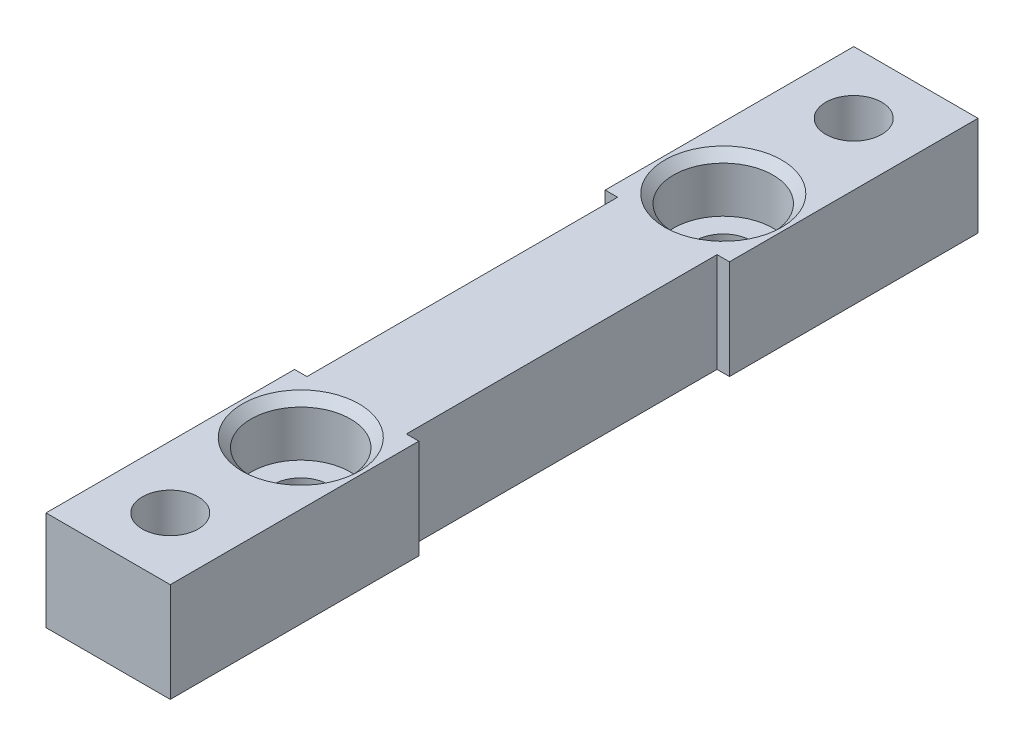
SolidWorks part; units mm, degrees
ref_plane "정면" through (0, 0, 0) normal (0, 0, 1) x (1, 0, 0)
ref_plane "윗면" through (0, 0, 0) normal (0, 1, 0) x (1, 0, 0)
ref_plane "우측면" through (0, 0, 0) normal (1, 0, 0) x (0, 0, -1)
sketch "스케치1" plane through (0, 0, 0) normal (0, 1, 0) x (1, 0, 0)
  line L0 (0, -17) -> (0, 17)
  line L14 (-5, 32.5) -> (5, 32.5)
  line L15 (-5, 32.5) -> (-5, 12.5)
  line L16 (-5, 12.5) -> (5, 12.5)
  line L17 (5, 32.5) -> (5, 12.5)
  line L18 (-5, 32.5) -> (5, 12.5) construction
  line L19 (-5, 12.5) -> (5, 32.5) construction
  line L20 (-4, 12.5) -> (4, 12.5)
  line L21 (-4, 12.5) -> (-4, -12.5)
  line L22 (-4, 0) -> (4, 0)
  line L23 (4, 12.5) -> (4, -12.5)
  line L24 (-4, 12.5) -> (4, 0) construction
  line L25 (-4, 0) -> (4, 12.5) construction
  line L26 (-4, 0) -> (4, -12.5) construction
  line L27 (-4, -12.5) -> (4, 0) construction
  line L28 (-5, -12.5) -> (5, -32.5) construction
  line L29 (-5, -32.5) -> (5, -12.5) construction
  line L30 (-4, -12.5) -> (4, -12.5)
  line L31 (5, -32.5) -> (5, -12.5)
  line L32 (-5, -12.5) -> (5, -12.5)
  line L33 (-5, -32.5) -> (-5, -12.5)
  line L34 (-5, -32.5) -> (5, -32.5)
  point P0 (0, 22.5)
  point P5 (0, 6.25)
  point P18 (0, -6.25)
  point P20 (0, 0)
  point P21 (0, -22.5)
  dimension "D1" = 10
  dimension "D2" = 20
  dimension "D3" = 32.5
  dimension "D4" = 8
  dimension "D5" = 17
extrude "보스-돌출1" add sketch "스케치1" along normal blind 8
hole_wizard "M4 육각 소켓 머리 캡 나사용 카운터보어1" positions "스케치2" profile "스케치3" counterbore size "M4" standard "ISO" end condition up to next
sketch "스케치2" plane through (0, 8, 0) normal (0, 1, 0) x (1, 0, 0)
  line L0 (0, 17) -> (0, -17)
  line L2 (4, 12.5) -> (4, -12.5) construction
  line L3 (4, 12.5) -> (4, -12.5)
  point P1 (0, 17)
  point P2 (0, -17)
  point P13 (4, 0)
  point P14 (0, 0)
  dimension "D1" = 34
sketch "스케치3" plane through (0, 8, -17) normal (1, 0, 0) x (0, 0, 1)
  line L0 (0, 0) -> (0, 8)
  line L1 (0, 8) -> (2.25, 8)
  line L3 (2.25, 8) -> (2.25, 4.4)
  line L4 (4, 4.4) -> (2.25, 4.4)
  line L5 (4, 4.4) -> (4, 0.7)
  line L6 (4, 0.7) -> (4.7, 0)
  line L7 (4.7, 0) -> (0, 0)
  line L8 (-4, 0.7) -> (-4.7, 0) construction
  line L11 (0, -6.35) -> (0, 107.95) construction
  dimension "관통 구멍 지름" = 4.5
  dimension "관통 구멍 깊이" = 8
  dimension "카운터보어 지름" = 8
  dimension "카운터보어 깊이" = 4.4
  dimension "표면 카운터싱크 지름" = 9.4
  dimension "표면 카운터싱크 각도" = 90
hole_wizard "M4 여유 구멍1" positions "스케치4" profile "스케치6" hole size "M4" standard "ISO" end condition up to next
sketch "스케치4" plane through (0, 0, 0) normal (0, -1, 0) x (-1, 0, 0)
  line L0 (0, -27.5) -> (0, 27.5)
  line L2 (-4, 12.5) -> (-4, -12.5) construction
  line L3 (-4, 12.5) -> (-4, -12.5)
  point P1 (0, -27.5)
  point P2 (0, 27.5)
  point P7 (0, 0)
  point P8 (-4, 0)
  point P13 (54.1084, -109.4208)
  dimension "D1" = 55
sketch "스케치6" plane through (0, 0, 27.5) normal (1, 0, 0) x (0, 0, -1)
  line L0 (0, 0) -> (0, 8)
  line L1 (0, 8) -> (2.25, 8)
  line L2 (2.25, 8) -> (2.25, 0)
  line L5 (2.25, 0) -> (0, 0)
  line L11 (0, -6.35) -> (0, 107.95) construction
  dimension "관통 구멍 지름" = 4.5
  dimension "관통 구멍 깊이" = 8
sketch "스케치7" plane through (0, 0, 0) normal (0, -1, 0) x (1, 0, 0)
  line L0 (-5, -32.5) -> (5, -32.5) construction
  line L1 (2.0496, -23.95) -> (-2.0496, -23.95)
  line L2 (-2.0496, -23.95) -> (-4.0992, -27.5)
  line L3 (-4.0992, -27.5) -> (-2.0496, -31.05)
  line L4 (-2.0496, -31.05) -> (2.0496, -31.05)
  line L5 (2.0496, -31.05) -> (4.0992, -27.5)
  line L6 (4.0992, -27.5) -> (2.0496, -23.95)
  line L7 (-4, 0) -> (4, 0)
  line L8 (-4, -12.5) -> (-4, 12.5) construction
  line L9 (4, -12.5) -> (4, 12.5) construction
  line L10 (4.0992, 27.5) -> (2.0496, 23.95)
  line L11 (2.0496, 31.05) -> (4.0992, 27.5)
  line L12 (-2.0496, 31.05) -> (2.0496, 31.05)
  line L13 (-4.0992, 27.5) -> (-2.0496, 31.05)
  line L14 (-2.0496, 23.95) -> (-4.0992, 27.5)
  line L15 (2.0496, 23.95) -> (-2.0496, 23.95)
  circle A0 centre (0, -27.5) radius 3.55 construction
  circle A1 centre (0, 27.5) radius 3.55 construction
  circle M4 centre (0, -27.5) radius 2.25
  circle M19 centre (0, 27.5) radius 2.25
  dimension "D1" = 7.1
extrude "컷-돌출1" cut sketch "스케치7" against normal blind 4 contours L5 L6 L1 L2 L3 L4 M4 | L15 L10 L11 L12 L13 L14 M19
